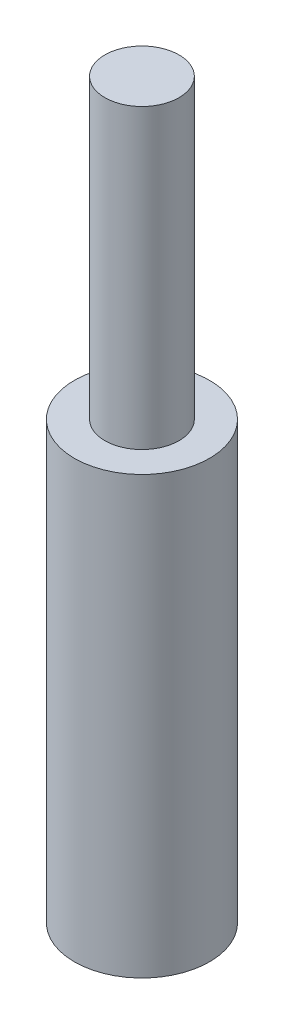
SolidWorks part; units mm, degrees
ref_plane "Front Plane" through (0, 0, 0) normal (0, 0, 1) x (1, 0, 0)
ref_plane "Top Plane" through (0, 0, 0) normal (0, 1, 0) x (1, 0, 0)
ref_plane "Right Plane" through (0, 0, 0) normal (1, 0, 0) x (0, 0, -1)
sketch "Sketch2" plane through (0, 0, 0) normal (0, 1, 0) x (1, 0, 0)
  circle A0 centre (0, 0) radius 1.55
  dimension "D1" = 3.1
extrude "Boss-Extrude1" add sketch "Sketch2" along normal blind 10
sketch "Sketch3" plane through (0, 10, 0) normal (0, 1, 0) x (1, 0, 0)
  circle A0 centre (0, 0) radius 0.85
  dimension "D1" = 1.7
extrude "Boss-Extrude2" add sketch "Sketch3" along normal blind 6.8129
